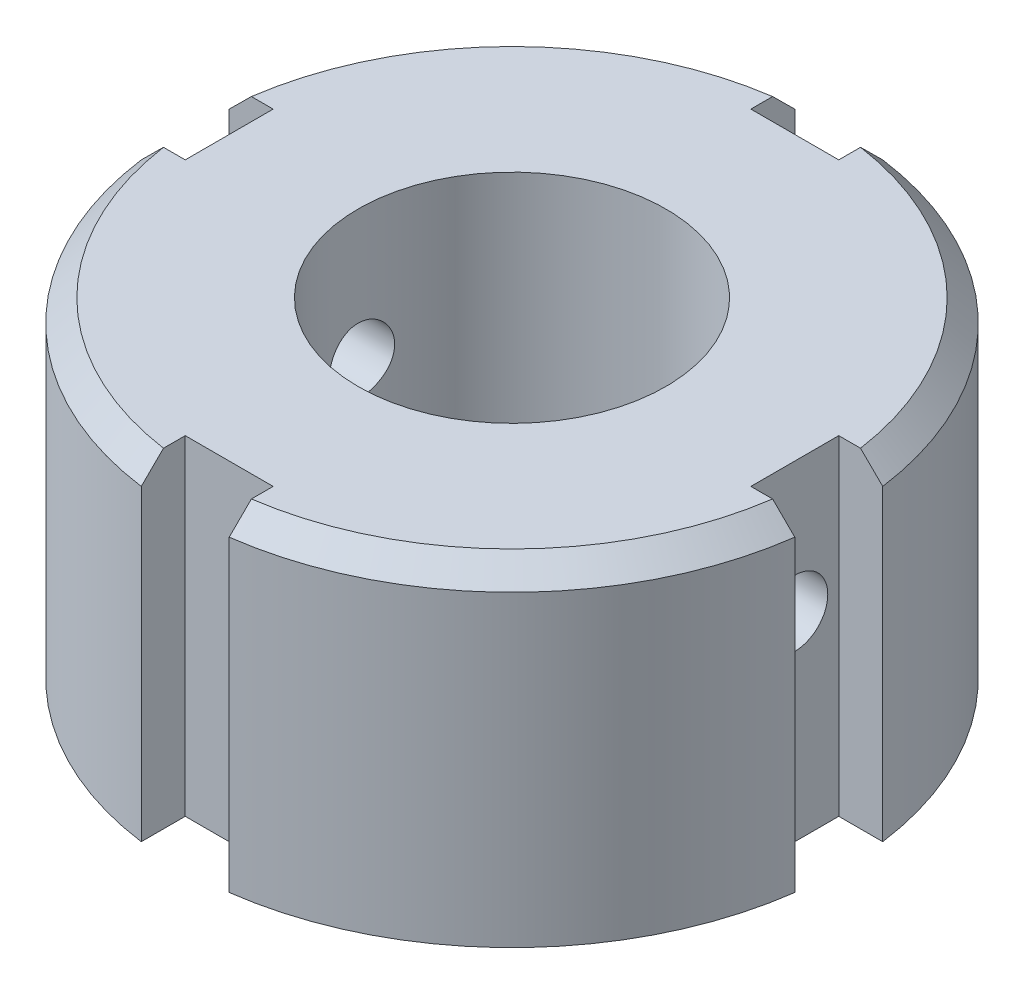
SolidWorks part; units mm, degrees
material "Plain Carbon Steel"
ref_plane "Front Plane" through (0, 0, 0) normal (0, 0, 1) x (1, 0, 0)
ref_plane "Top Plane" through (0, 0, 0) normal (0, 1, 0) x (1, 0, 0)
ref_plane "Right Plane" through (0, 0, 0) normal (1, 0, 0) x (0, 0, -1)
sketch "Sketch1" plane through (0, 0, 0) normal (0, 1, 0) x (1, 0, 0)
  circle A0 centre (0, 0) radius 15
  dimension "D1" = 30
extrude "Boss-Extrude1" add sketch "Sketch1" along normal mid plane 15
sketch "Sketch2" plane through (0, 0, 0) normal (0, 1, 0) x (1, 0, 0)
  line L0 (-2, 14.8661) -> (-2, 12.8661)
  line L1 (-2, 12.8661) -> (2, 12.8661)
  line L2 (2, 12.8661) -> (2, 14.8661)
  line L3 (14.8661, 2) -> (12.8661, 2)
  line L4 (12.8661, 2) -> (12.8661, -2)
  line L5 (12.8661, -2) -> (14.8661, -2)
  line L6 (2, -14.8661) -> (2, -12.8661)
  line L7 (2, -12.8661) -> (-2, -12.8661)
  line L8 (-2, -12.8661) -> (-2, -14.8661)
  line L9 (-14.8661, -2) -> (-12.8661, -2)
  line L10 (-12.8661, -2) -> (-12.8661, 2)
  line L11 (-12.8661, 2) -> (-14.8661, 2)
  circle A0 centre (0, 0) radius 15 construction
  arc A1 (2, 14.8661) -> (-2, 14.8661) centre (0, 0) ccw
  arc A2 (14.8661, -2) -> (14.8661, 2) centre (0, 0) ccw
  arc A3 (-2, -14.8661) -> (2, -14.8661) centre (0, 0) ccw
  arc A4 (-14.8661, 2) -> (-14.8661, -2) centre (0, 0) ccw
  point P23 (0, 0)
  dimension "D1" = 2
  dimension "D2" = 2
  dimension "D3" = 4
extrude "Cut-Extrude1" cut sketch "Sketch2" against normal through all both and the other way through all
chamfer "Chamfer1" distance 1 angle 45 4 edges at (-10.6066, 7.5, -10.6066) (10.6066, 7.5, -10.6066) (10.6066, 7.5, 10.6066) (-10.6066, 7.5, 10.6066)
sketch "Sketch3" plane through (0, 7.5, 0) normal (0, 1, 0) x (1, 0, 0)
  point P0 (0, 0)
hole_wizard "M16 Tapped Hole1" positions "Sketch3" profile "Sketch4" tap size "M16" standard "ISO" end condition up to next
sketch "Sketch4" plane through (0, 7.5, 0) normal (1, 0, 0) x (0, 0, 1)
  line L0 (0, 0) -> (0, 15)
  line L1 (0, 15) -> (7, 15)
  line L2 (7, 15) -> (7, 0)
  line L5 (7, 0) -> (0, 0)
  line L11 (0, -6.35) -> (0, 107.95) construction
  dimension "Thru Tap Drill Dia." = 14
  dimension "Thru Tap Drill Depth" = 15
cosmetic thread "Hole Thread1" parameters "D2"=16
sketch "Sketch5" plane through (12.8661, 0, 0) normal (1, 0, 0) x (0, 0, -1)
  line L0 (2, 7.5) -> (-2, 7.5) construction
  circle A0 centre (0, 1.5) radius 1.5
  point P5 (0, 0)
  dimension "D1" = 3
  dimension "D2" = 6
extrude "Cut-Extrude2" cut sketch "Sketch5" against normal through all both and the other way through all
